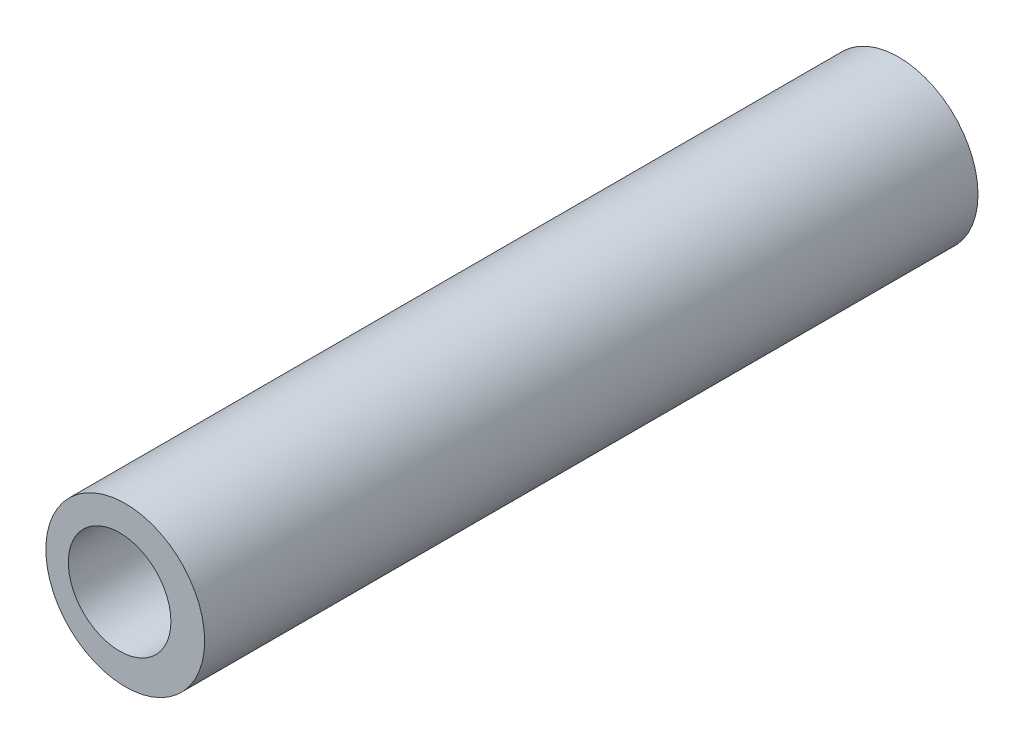
SolidWorks part; units mm, degrees
ref_plane "Front Plane" through (0, 0, 0) normal (0, 0, 1) x (1, 0, 0)
ref_plane "Top Plane" through (0, 0, 0) normal (0, 1, 0) x (1, 0, 0)
ref_plane "Right Plane" through (0, 0, 0) normal (1, 0, 0) x (0, 0, -1)
sketch "Sketch2" plane through (0, 0, 0) normal (0, 0, 1) x (1, 0, 0)
  circle A0 centre (0, 0) radius 84.7117
  circle A1 centre (-6.0123, 0) radius 54.721
extrude "Boss-Extrude2" add sketch "Sketch2" along normal blind 825
